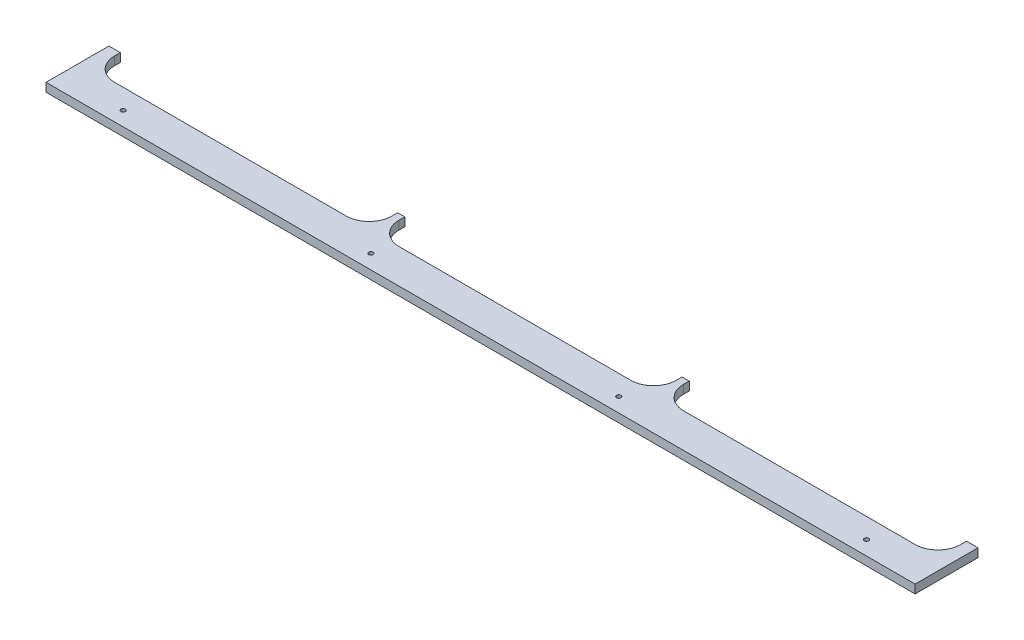
SolidWorks part; units mm, degrees
material "PC High Viscosity"
ref_plane "Front Plane" through (0, 0, 0) normal (0, 0, 1) x (1, 0, 0)
ref_plane "Top Plane" through (0, 0, 0) normal (0, 1, 0) x (1, 0, 0)
ref_plane "Right Plane" through (0, 0, 0) normal (1, 0, 0) x (0, 0, -1)
sketch "Sketch1" plane through (0, 0, 0) normal (0, 1, 0) x (1, 0, 0)
  line L1 (0, 0) -> (965.2, 0)
  line L2 (0, 0) -> (0, 69.85)
  line L4 (965.2, 0) -> (965.2, 69.85)
  line L18 (328.6125, 69.85) -> (328.6125, 63.5)
  line L19 (354.0125, 38.1) -> (611.1875, 38.1)
  line L20 (636.5875, 69.85) -> (636.5875, 63.5)
  line L21 (669.925, 38.1) -> (927.1, 38.1)
  line L22 (644.525, 63.5) -> (644.525, 69.85)
  line L24 (952.5, 63.5) -> (952.5, 69.85)
  line L27 (636.5875, 69.85) -> (644.525, 69.85)
  line L30 (328.6125, 69.85) -> (320.675, 69.85)
  line L31 (952.5, 69.85) -> (965.2, 69.85)
  line L32 (69.85, 15.875) -> (345.0158, 15.875) construction
  line L33 (12.7, 69.85) -> (0, 69.85)
  line L35 (12.7, 69.85) -> (12.7, 63.5)
  line L36 (38.1, 38.1) -> (295.275, 38.1)
  line L37 (320.675, 69.85) -> (320.675, 63.5)
  line L38 (482.6, 0) -> (482.6, 38.1) construction
  arc A0 (328.6125, 63.5) -> (354.0125, 38.1) centre (354.0125, 63.5) ccw
  arc A1 (611.1875, 38.1) -> (636.5875, 63.5) centre (611.1875, 63.5) ccw
  arc A2 (669.925, 38.1) -> (644.525, 63.5) centre (669.925, 63.5) cw
  arc A3 (927.1, 38.1) -> (952.5, 63.5) centre (927.1, 63.5) ccw
  circle A8 centre (69.85, 15.875) radius 2.4574
  circle A9 centre (345.0158, 15.875) radius 2.4575
  arc A11 (295.275, 38.1) -> (320.675, 63.5) centre (295.275, 63.5) ccw
  arc A12 (12.7, 63.5) -> (38.1, 38.1) centre (38.1, 63.5) ccw
  circle A13 centre (895.35, 15.875) radius 2.4574
  circle A14 centre (620.1842, 15.875) radius 2.4575
  point P17 (320.675, 38.1)
  point P34 (12.7, 38.1)
  dimension "D4" = 25.4
  dimension "D5" = 4.9149
  dimension "D18" = 25.4
  dimension "D1" = 965.2
  dimension "D2" = 15.875
  dimension "D3" = 69.85
  dimension "D6" = 307.975
  dimension "D7" = 307.975
  dimension "D8" = 2
  dimension "D9" = 7.9375
  dimension "D10" = 12.7
  dimension "D11" = 38.1
  dimension "D12" = 275.1658
  dimension "D13" = 31.75
  dimension "D14" = 7.9375
  dimension "D15" = 307.975
  dimension "D16" = 69.85
  dimension "D17" = 38.1
  dimension "D19" = 38.1
extrude "Boss-Extrude1" add sketch "Sketch1" along normal blind 9.525
fillet "Fillet1" [suppressed] radius 3.175
